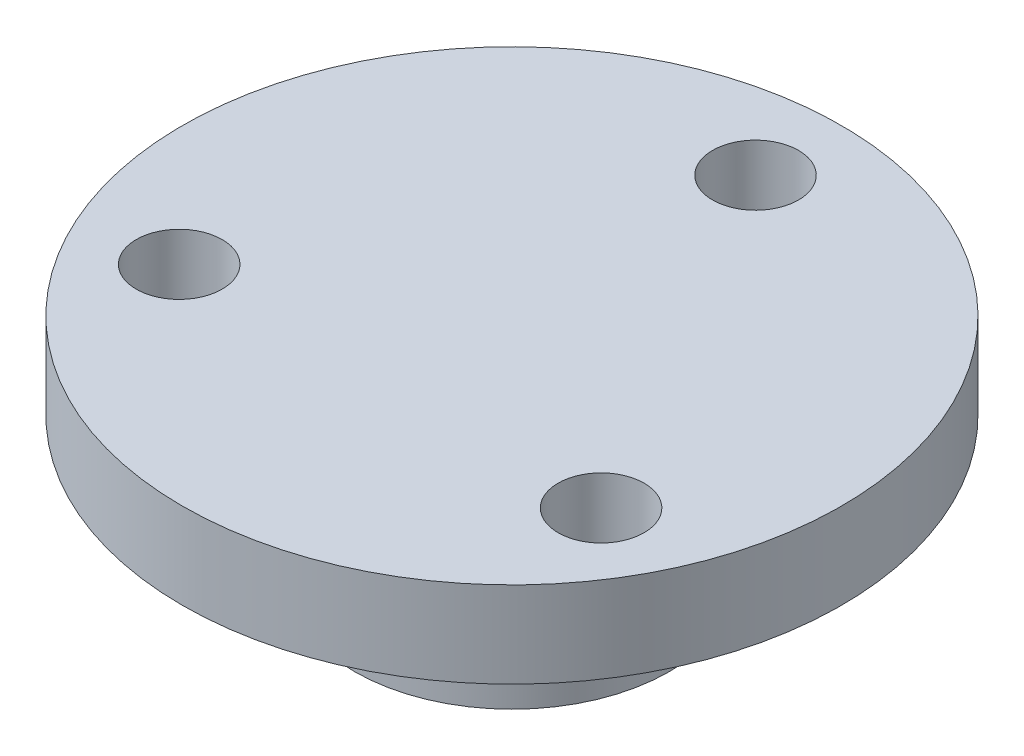
SolidWorks part; units mm, degrees
ref_plane "Front Plane" through (0, 0, 0) normal (0, 0, 1) x (1, 0, 0)
ref_plane "Top Plane" through (0, 0, 0) normal (0, 1, 0) x (1, 0, 0)
ref_plane "Right Plane" through (0, 0, 0) normal (1, 0, 0) x (0, 0, -1)
sketch "Sketch1" plane through (0, 0, 0) normal (0, 1, 0) x (1, 0, 0)
  line L0 (-1.095, -1.0252) -> (1.095, -1.0252)
  line L1 (0, 6.5888) -> (0, -8.3668) construction
  line L3 (-2, -2.0252) -> (2, -2.0252)
  line L4 (-2, -2.0252) -> (-2, -4.0252)
  line L5 (-2, -4.0252) -> (2, -4.0252)
  line L6 (2, -2.0252) -> (2, -4.0252)
  line L7 (-2, -2.0252) -> (2, -4.0252) construction
  line L8 (-2, -4.0252) -> (2, -2.0252) construction
  arc A0 (1.095, -1.0252) -> (-1.095, -1.0252) centre (0, 0) ccw
  circle A1 centre (0, 0) radius 5.5
  point P7 (0, -3.0252)
  dimension "D1" = 3
  dimension "D6" = 11
  dimension "D2" = 2.19
  dimension "D3" = 2
  dimension "D4" = 4
  dimension "D5" = 1
extrude "Boss-Extrude1" add sketch "Sketch1" along normal blind 5
sketch "Sketch2" plane through (0, 5, 0) normal (0, 1, 0) x (1, 0, 0)
  line L0 (0, 20.7918) -> (0, -25.7458) construction
  circle A0 centre (0, 0) radius 11.5
  dimension "D1" = 23
extrude "Boss-Extrude2" add sketch "Sketch2" along normal blind 3 contours A0
sketch "Sketch3" plane through (0, 5, 0) normal (0, -1, 0) x (1, 0, 0)
  line L0 (0, 14.7277) -> (0, -15.4684) construction
  circle A0 centre (0, -8.5) radius 1.5
  dimension "D1" = 3
  dimension "D2" = 8.5
extrude "wheel_screws" cut sketch "Sketch3" against normal blind 3
pattern_circular "wheel_screw_pattern" count 3 every 120 about axis through (0, 0, 0) along (0, 1, 0) of "wheel_screws"
sketch "Sketch5" plane through (0, 0, 4.0252) normal (0, 0, -1) x (-1, 0, 0)
  line L0 (2, 5) -> (-2, 5) construction
  circle A0 centre (0, 2.5) radius 0.95
  dimension "D1" = 1.9
  dimension "D2" = 2.5
extrude "motor_screw_hole" cut sketch "Sketch5" along normal blind 3 and the other way through all
